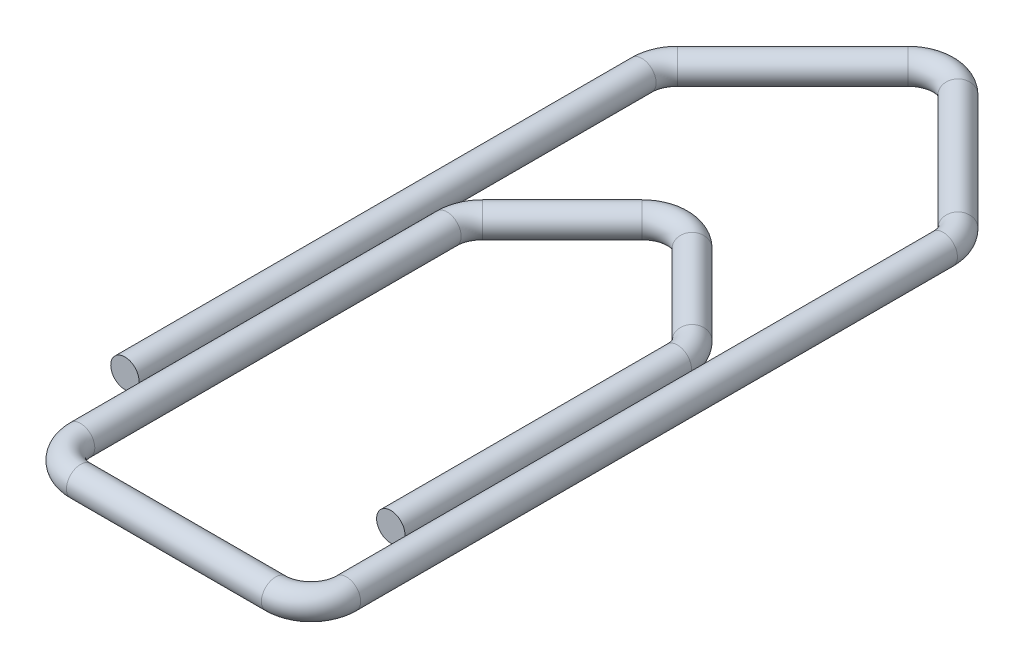
SolidWorks part; units mm, degrees
ref_plane "Front Plane" through (0, 0, 0) normal (0, 0, 1) x (1, 0, 0)
ref_plane "Top Plane" through (0, 0, 0) normal (0, 1, 0) x (1, 0, 0)
ref_plane "Right Plane" through (0, 0, 0) normal (1, 0, 0) x (0, 0, -1)
sketch "Sketch1" plane through (0, 0, 0) normal (0, 1, 0) x (1, 0, 0)
  line L0 (0, 0) -> (0, 29.1716)
  line L1 (0.5858, 30.5858) -> (7.0858, 37.0858)
  line L2 (9.9142, 37.0858) -> (16.4142, 30.5858)
  line L3 (17, 29.1716) -> (17, -4.5)
  line L4 (15, -6.5) -> (4, -6.5)
  line L5 (2, -4.5) -> (2, 16.1716)
  line L6 (2.5858, 17.5858) -> (7.0858, 22.0858)
  line L7 (9.9142, 22.0858) -> (14.4142, 17.5858)
  line L8 (15, 16.1716) -> (15, 0)
  line L9 (8.5, 37.2556) -> (8.5, -35.8926) construction
  arc A0 (4, -6.5) -> (2, -4.5) centre (4, -4.5) cw
  arc A1 (17, -4.5) -> (15, -6.5) centre (15, -4.5) cw
  arc A2 (14.4142, 17.5858) -> (15, 16.1716) centre (13, 16.1716) cw
  arc A3 (2, 16.1716) -> (2.5858, 17.5858) centre (4, 16.1716) cw
  arc A4 (7.0858, 22.0858) -> (9.9142, 22.0858) centre (8.5, 20.6716) cw
  arc A5 (16.4142, 30.5858) -> (17, 29.1716) centre (15, 29.1716) cw
  arc A6 (0, 29.1716) -> (0.5858, 30.5858) centre (2, 29.1716) cw
  arc A7 (7.0858, 37.0858) -> (9.9142, 37.0858) centre (8.5, 35.6716) cw
  point P13 (0, 0)
  point P14 (0, 0)
  point P15 (0, 0)
  point P16 (0, 0)
  point P19 (2, -6.5)
  point P22 (17, -6.5)
  point P25 (15, 17)
  point P28 (2, 17)
  point P31 (8.5, 23.5)
  point P34 (17, 30)
  point P37 (0, 30)
  point P40 (8.5, 38.5)
  dimension "D6" = 2
  dimension "D1" = 45
  dimension "D2" = 30
  dimension "D3" = 30
  dimension "D4" = 15
  dimension "D5" = 17
sketch "Sketch2" plane through (0, 0, 0) normal (0, 0, 1) x (1, 0, 0)
  circle A0 centre (0, 0) radius 0.8
  dimension "D1" = 1.6
sweep "Sweep1" add profiles "Sketch2" path "Sketch1"
